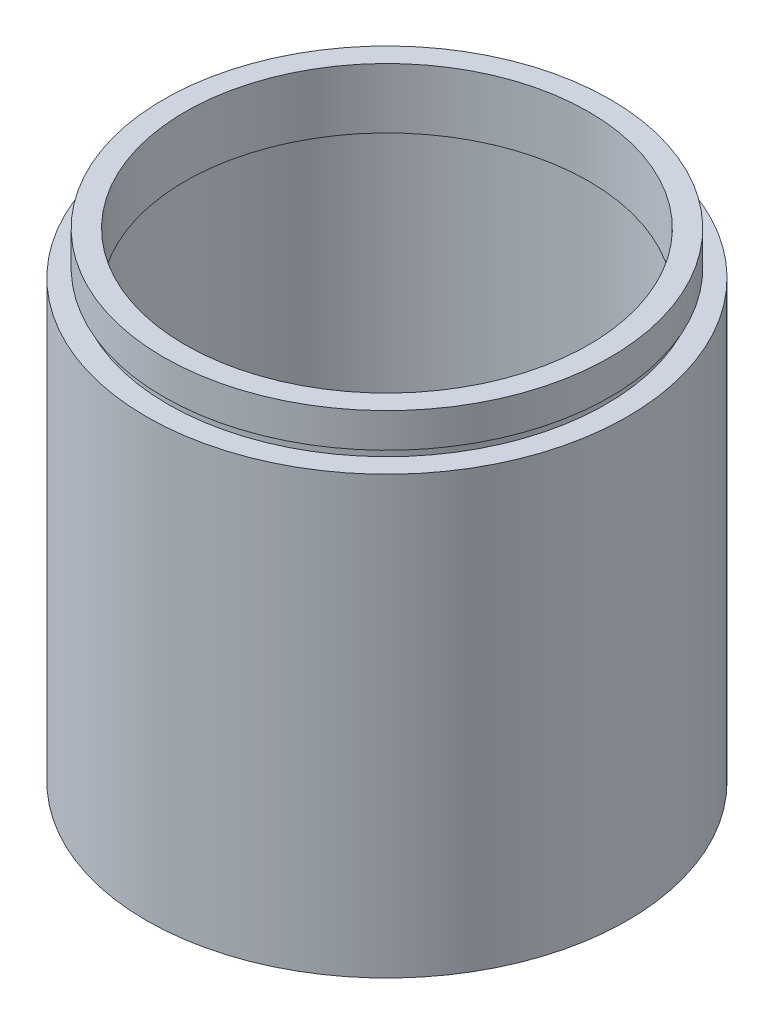
SolidWorks part; units mm, degrees
ref_plane "前视基准面" through (0, 0, 0) normal (0, 0, 1) x (1, 0, 0)
ref_plane "上视基准面" through (0, 0, 0) normal (0, 1, 0) x (1, 0, 0)
ref_plane "右视基准面" through (0, 0, 0) normal (1, 0, 0) x (0, 0, -1)
sketch "草图1" plane through (0, 0, 0) normal (0, 0, 1) x (1, 0, 0)
  line L0 (0, 161.3762) -> (0, 0) construction
  line L1 (141.7365, 0) -> (-131.7984, 0) construction
  line L2 (23.5, 55.8) -> (26, 55.8)
  line L3 (26, 55.8) -> (26, 51.8)
  line L4 (26, 51.8) -> (25.5, 51.8)
  line L5 (25.5, 51.8) -> (25.5, 50.8)
  line L6 (25.5, 50.8) -> (28, 50.8)
  line L7 (28, 50.8) -> (28, 0)
  line L8 (28, 0) -> (25.5, 0)
  line L9 (25.5, 0) -> (25.5, 47.8)
  line L10 (25.5, 47.8) -> (26.1, 47.8)
  line L11 (26.1, 47.8) -> (26.1, 48.8)
  line L12 (26.1, 48.8) -> (23.5, 48.8)
  line L13 (23.5, 48.8) -> (23.5, 55.8)
  dimension "D1" = 23.5
  dimension "D2" = 26
  dimension "D3" = 1
  dimension "D4" = 1
  dimension "D5" = 25.5
  dimension "D6" = 26.1
  dimension "D7" = 25.5
  dimension "D8" = 5
  dimension "D9" = 7
  dimension "D10" = 50.8
  dimension "D11" = 28
revolve "旋转1" add sketch "草图1" angle 360 about L0
cosmetic thread "装饰螺纹线1" parameters "D2"=52
cosmetic thread "装饰螺纹线2" parameters "D2"=48
cosmetic thread "装饰螺纹线3" parameters "D2"=51
